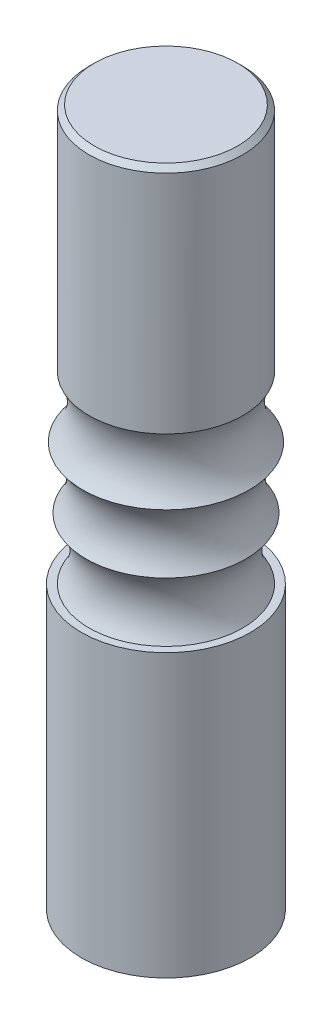
SolidWorks part; units mm, degrees
ref_plane "Plan de face" through (0, 0, 0) normal (0, 0, 1) x (1, 0, 0)
ref_plane "Plan de dessus" through (0, 0, 0) normal (0, 1, 0) x (1, 0, 0)
ref_plane "Plan de droite" through (0, 0, 0) normal (1, 0, 0) x (0, 0, -1)
sketch "Esquisse1" plane through (0, 0, 0) normal (0, 1, 0) x (1, 0, 0)
  circle A0 centre (0, 0) radius 16.5
  dimension "D1" = 33
extrude "Boss.-Extru.1" add sketch "Esquisse1" along normal blind 55
sketch "Esquisse3" plane through (0, 55, 0) normal (0, 1, 0) x (1, 0, 0)
  circle A0 centre (0, 0) radius 15
  dimension "D1" = 30
sketch "Esquisse4" plane through (0, 0, 0) normal (0, 0, 1) x (1, 0, 0)
  line L0 (0, 55) -> (0, 136) construction
  line L1 (15, 55) -> (-15, 55) construction
  line L2 (0, 55) -> (15, 55)
  line L3 (15, 136) -> (15, 90.9024)
  line L4 (15, 136) -> (0, 136)
  line L5 (0, 55) -> (0, 136)
  arc A0 (15, 55) -> (15.6109, 66.9844) centre (23, 60.6) cw
  arc A1 (15.6109, 66.9844) -> (16.2481, 78.9675) centre (23, 72.6) cw
  arc A2 (16.2481, 78.9675) -> (15, 90.9024) centre (23.5807, 85.767) cw
  point P9 (0, 0)
  dimension "D1" = 81
  dimension "D2" = 12
  dimension "D5" = 12
  dimension "D6" = 12
revolve "Révolution1" add sketch "Esquisse4" angle 360 about L0
chamfer "Chanfrein1" distance 1 angle 45 1 edges at (0, 136, -15)
